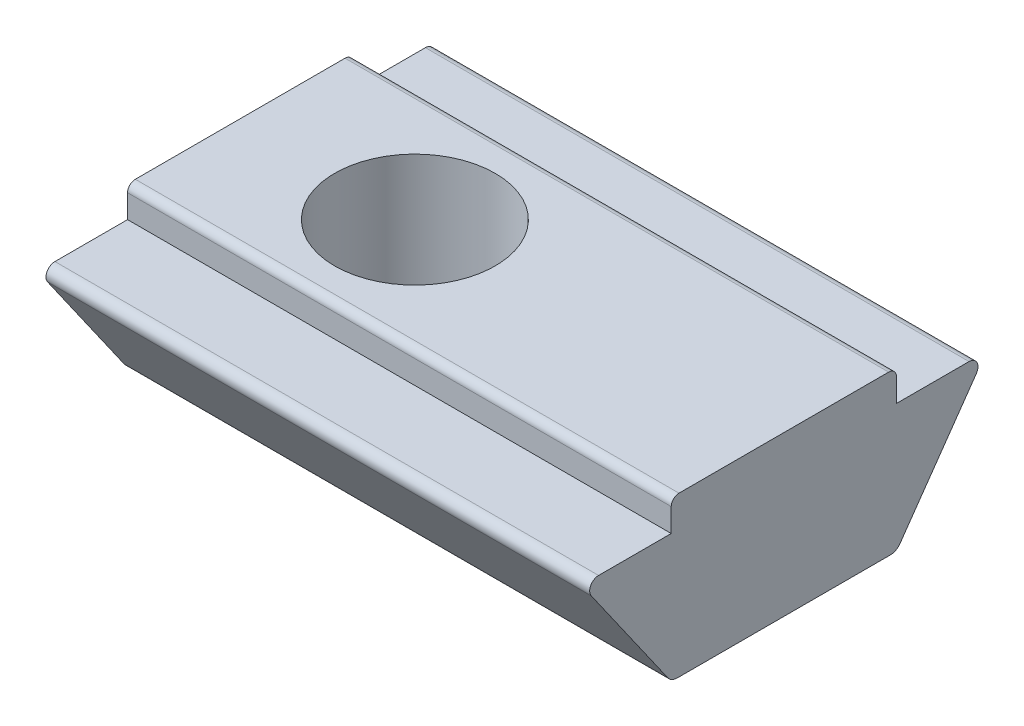
SolidWorks part; units mm, degrees
ref_plane "Front Plane" through (0, 0, 0) normal (0, 0, 1) x (1, 0, 0)
ref_plane "Top Plane" through (0, 0, 0) normal (0, 1, 0) x (1, 0, 0)
ref_plane "Right Plane" through (0, 0, 0) normal (1, 0, 0) x (0, 0, -1)
ref_plane "Plane1" through (-4.5, 0, 0) normal (1, 0, 0) x (0, 0, -1)
ref_plane "Plane2" through (6, 0, 0) normal (1, 0, 0) x (0, 0, -1)
sketch "Sketch1" plane through (-4.5, 0, 0) normal (1, 0, 0) x (0, 0, -1)
  line L0 (2.9, 0) -> (-2.9, 0)
  line L1 (-2.9, 0) -> (-2.9, -0.8)
  line L2 (-2.9, -0.8) -> (-4.77, -0.8)
  line L3 (5, 0) -> (5, -4.1) construction
  line L4 (-4.9584, -1.162) -> (-2.9, -4.1)
  line L5 (-2.9, -4.1) -> (2.9, -4.1)
  line L6 (2.9, -4.1) -> (4.9584, -1.162)
  line L7 (-5, 0) -> (-5, -4.1) construction
  line L8 (4.77, -0.8) -> (2.9, -0.8)
  line L9 (2.9, -0.8) -> (2.9, 0)
  line L10 (0, 0) -> (0, -4.1) construction
  arc A2 (-4.9584, -1.162) -> (-4.77, -0.8) centre (-4.77, -1.03) cw
  arc A3 (4.9584, -1.162) -> (4.77, -0.8) centre (4.77, -1.03) ccw
  point P18 (-2.9, -4.1)
  point P21 (2.9, -4.1)
  dimension "FIX_4" = 0.23
  dimension "FIX_2" = 5.8
  dimension "T" = 4.1
  dimension "FIX_3" = 3.3
  dimension "FIX_1" = 10
  dimension "FIX_5" = 5.8
extrude "Boss-Extrude1" add sketch "Sketch1" along normal blind 14
fillet "Fillet1" radius 0.3 2 edges at (2.5, -4.1, 2.9) (2.5, -4.1, -2.9)
fillet "Fillet2" radius 0.2 2 edges at (2.5, 0, 2.9) (2.5, 0, -2.9)
sketch "Sketch2" plane through (6, 0, 0) normal (1, 0, 0) x (0, 0, -1)
  line L0 (0, 1.6655) -> (0, -9.505) construction
  line L2 (0, -3.9) -> (2.1, -3.9)
  line L3 (0, -3.9) -> (0, -4.1)
  line L4 (0, -4.1) -> (2.1, -4.1)
  line L5 (2.1, -3.9) -> (2.1, -4.1)
  dimension "FIX_10" = 0.2
  dimension "FIX_9" = 2.1
  dimension "T" = 4.1
revolve "Cut-Revolve1" cut sketch "Sketch2" angle 360 about L0
sketch "Sketch3" plane through (6, 0, 0) normal (1, 0, 0) x (0, 0, -1)
  line L0 (0, 0) -> (0, -4.8) construction
  line L1 (1.6703, -3.9) -> (0, -3.9) construction
  line L2 (1.6703, -4.8) -> (0, -4.8) construction
  line L3 (1.6703, -3.9) -> (0, -3.9)
  line L4 (0, -3.9) -> (0, -4.8)
  arc A0 (0, -4.8) -> (1.6703, -3.9) centre (0, -2.8) ccw
  dimension "FIX_12" = 4
  dimension "KSS_1" = 4.8
  dimension "KSS_2" = 3.9
revolve "Revolve1" add sketch "Sketch3" angle 360 about L0
hole_wizard "Tapped Hole1" positions "Sketch5" profile "Sketch4" tap size "M5x0.8" standard "JIS" end condition through all
sketch "Sketch5" plane through (0, 0, 0) normal (0, 1, 0) x (1, 0, 0)
  point P0 (0, 0)
sketch "Sketch4" plane through (0, 0, 0) normal (1, 0, 0) x (0, 0, 1)
  line L0 (0, 0) -> (0, 4.8)
  line L1 (0, 4.8) -> (2.067, 4.8)
  line L2 (2.067, 4.8) -> (2.067, 0)
  line L5 (2.067, 0) -> (0, 0)
  line L11 (0, 0) -> (0, 4.8) construction
  dimension "Thru Tap Drill Dia." = 4.134
  dimension "Thru Tap Drill Depth" = 4.8
cosmetic thread "Thread1" parameters "NFIX_1"=5
equation "\"KSS_1@Sketch3\" = \"T@Sketch1\" + 0.7"
equation "\"KSS_2@Sketch3\"= \"T@Sketch1\" - 0.2"
